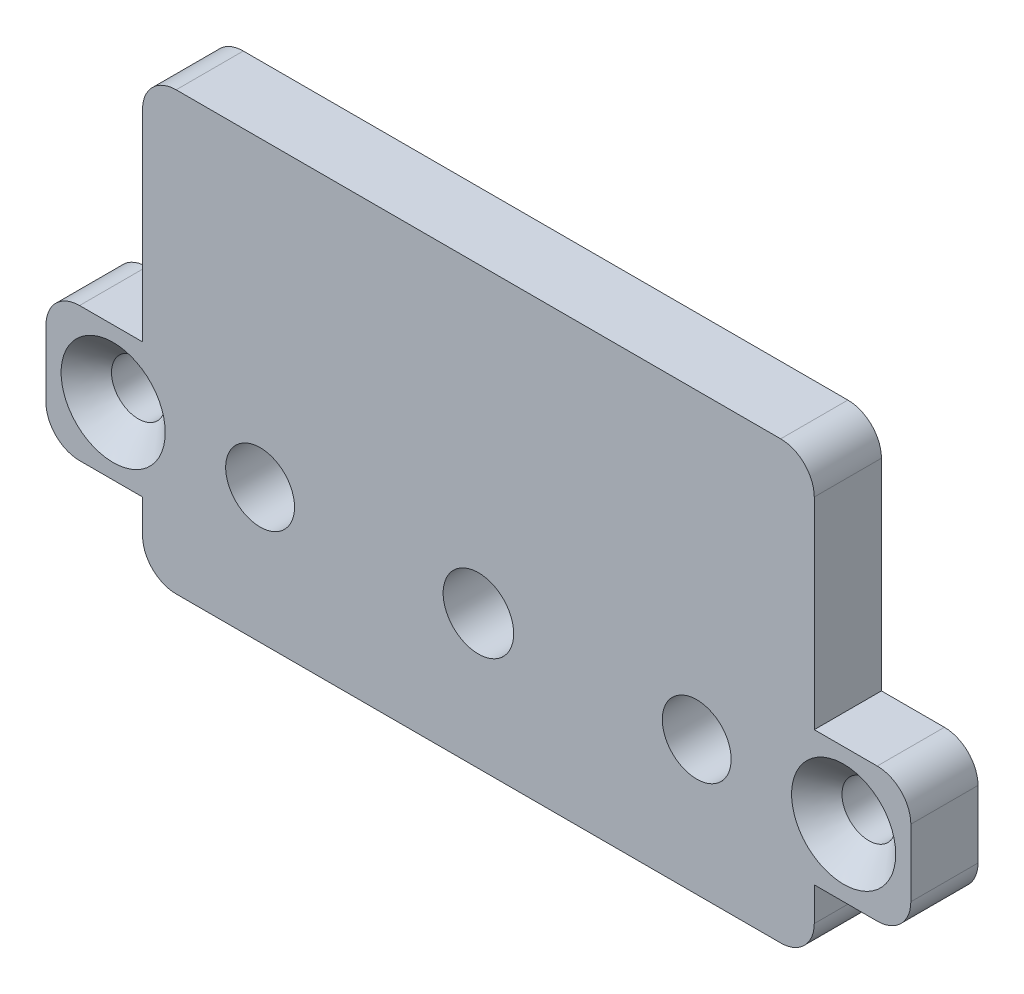
SolidWorks part; units mm, degrees
ref_plane "Спереди" through (0, 0, 0) normal (0, 0, 1) x (1, 0, 0)
ref_plane "Сверху" through (0, 0, 0) normal (0, 1, 0) x (1, 0, 0)
ref_plane "Справа" through (0, 0, 0) normal (1, 0, 0) x (0, 0, -1)
sketch "Эскиз1" plane through (0, 0, 0) normal (0, 0, 1) x (1, 0, 0)
  line L0 (38.75, 4) -> (12.75, 4)
  line L1 (0, 0) -> (51.5, 0)
  line L2 (0, 0) -> (0, 8)
  line L3 (0, 8) -> (51.5, 8)
  line L4 (51.5, 0) -> (51.5, 8)
  line L6 (5.75, -4) -> (45.75, -4)
  line L7 (5.75, -4) -> (5.75, 22)
  line L8 (5.75, 22) -> (45.75, 22)
  line L9 (45.75, -4) -> (45.75, 22)
  circle A0 centre (4, 4) radius 1.6
  circle A1 centre (47.5, 4) radius 1.6
  circle A2 centre (25.75, 4) radius 2.1
  circle A3 centre (12.75, 4) radius 2.05
  circle A4 centre (38.75, 4) radius 2.05
  point P9 (25.75, 8)
  point P10 (51.5, 4)
  point P17 (25.75, 22)
  point P21 (25.75, 4)
  dimension "D2" = 3.2
  dimension "D3" = 3.2
  dimension "D7" = 4.2
  dimension "D9" = 4.1
  dimension "D10" = 4.1
  dimension "D1" = 8
  dimension "D4" = 43.5
  dimension "D5" = 4
  dimension "D6" = 4
  dimension "D8" = 26
  dimension "D11" = 8
  dimension "D12" = 40
  dimension "D13" = 18
extrude "Бобышка-Вытянуть1" add sketch "Эскиз1" along normal blind 4
fillet "Скругление1" radius 2 4 edges at (51.5, 0, 2) (51.5, 8, 2) (0, 0, 2) (0, 8, 2)
chamfer "Фаска1" distance 1.5 angle 45 2 edges at (49.1, 4, 4) (5.6, 4, 4)
fillet "Скругление2" radius 2 4 edges at (45.75, -4, 2) (5.75, -4, 2) (5.75, 22, 2) (45.75, 22, 2)
